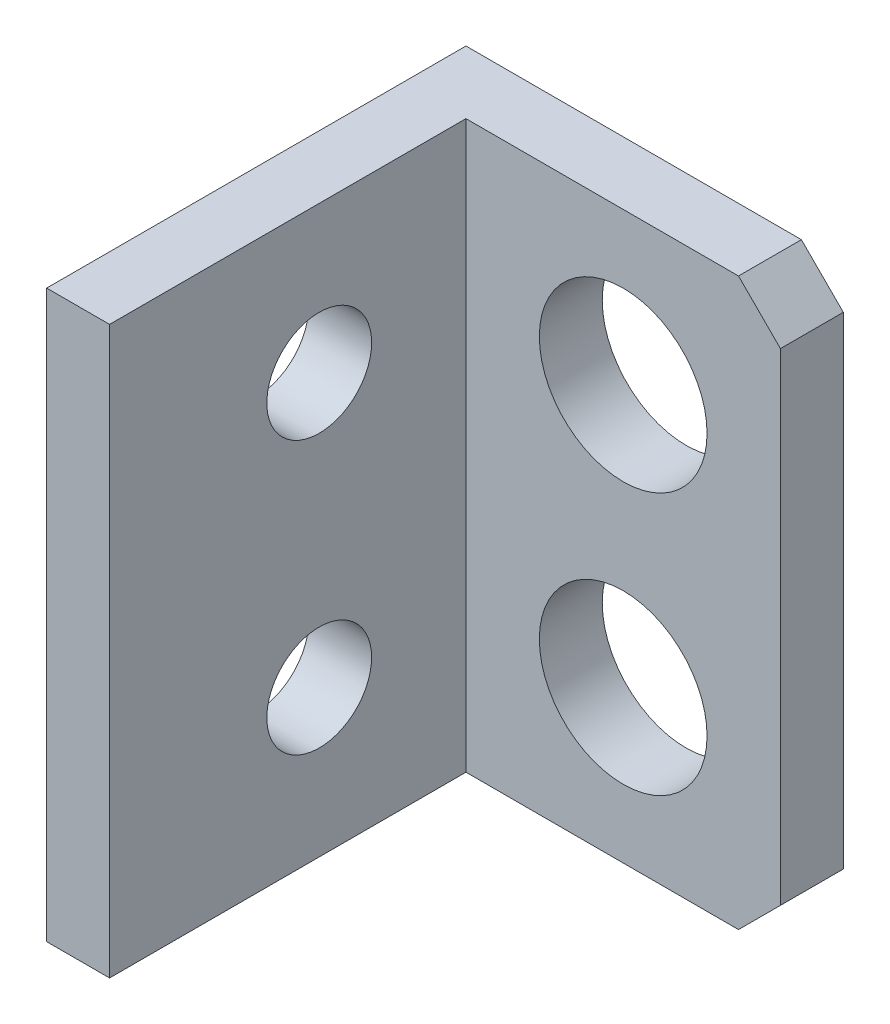
SolidWorks part; units mm, degrees
ref_plane "Front Plane" through (0, 0, 0) normal (0, 0, 1) x (1, 0, 0)
ref_plane "Top Plane" through (0, 0, 0) normal (0, 1, 0) x (1, 0, 0)
ref_plane "Right Plane" through (0, 0, 0) normal (1, 0, 0) x (0, 0, -1)
sketch "Sketch1" plane through (0, 0, 0) normal (1, 0, 0) x (0, 0, -1)
  line L1 (0, 0) -> (20, 0)
  line L2 (0, 0) -> (0, 27)
  line L3 (0, 27) -> (20, 27)
  line L4 (20, 0) -> (20, 27)
  circle A0 centre (10, 7) radius 2.5
  circle A2 centre (10, 20) radius 2.5
extrude "Boss-Extrude1" add sketch "Sketch1" along normal blind 3
sketch "Sketch2" plane through (3, 0, 0) normal (1, 0, 0) x (0, 0, -1)
  line L0 (0, 0) -> (20, 0) construction
  line L1 (20, 27) -> (17, 27)
  line L2 (20, 27) -> (20, 0)
  line L3 (20, 0) -> (17, 0)
  line L4 (17, 27) -> (17, 0)
extrude "Boss-Extrude2" add sketch "Sketch2" along normal blind 15
sketch "Sketch3" plane through (0, 0, -20) normal (0, 0, -1) x (-1, 0, 0)
  circle A0 centre (-10.5, 19.75) radius 4
  circle A1 centre (-10.5, 7.25) radius 4
  point P10 (0, 0)
extrude "Cut-Extrude1" cut sketch "Sketch3" against normal blind 15
chamfer "Chamfer1" distance 2 angle 45 2 edges at (18, 0, -18.5) (18, 27, -18.5)
